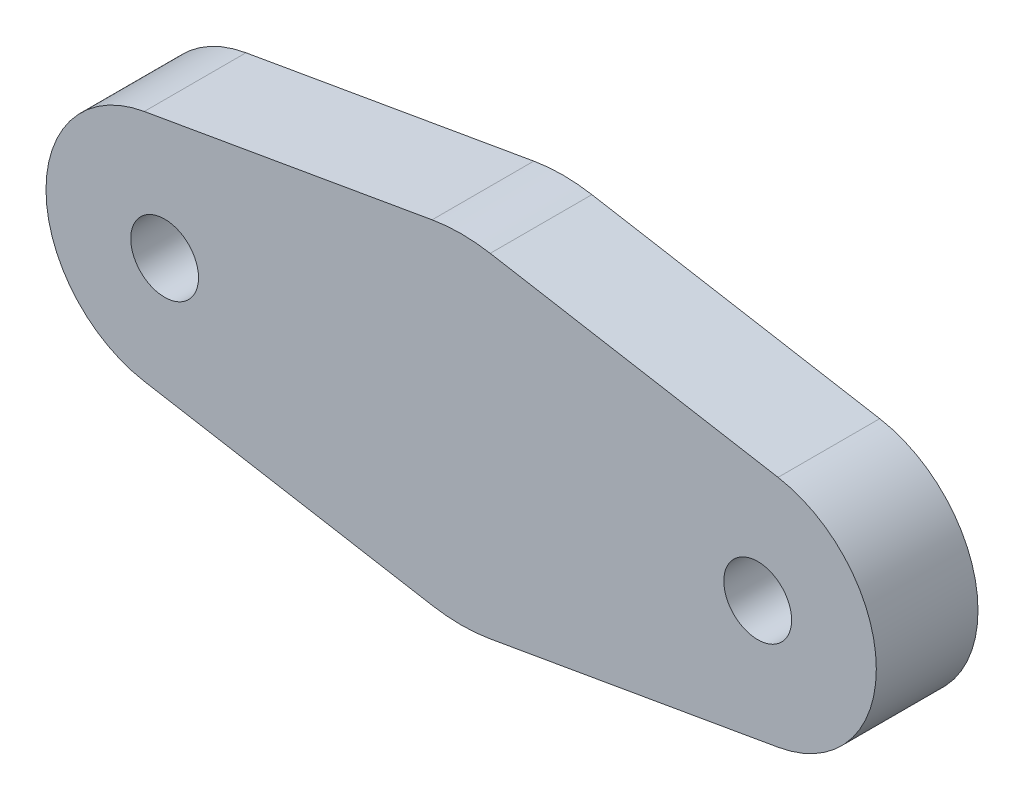
SolidWorks part; units mm, degrees
material "Birch plywood FK"
ref_plane "Спереди" through (0, 0, 0) normal (0, 0, 1) x (1, 0, 0)
ref_plane "Сверху" through (0, 0, 0) normal (0, 1, 0) x (1, 0, 0)
ref_plane "Справа" through (0, 0, 0) normal (1, 0, 0) x (0, 0, -1)
sketch "Эскиз1" plane through (0, 0, 0) normal (0, 0, 1) x (1, 0, 0)
  line L0 (-1.7143, 9.852) -> (-18.7, 6.8964)
  line L1 (-17.5, 0) -> (17.5, 0) construction
  line L2 (18.7, 6.8964) -> (1.7143, 9.852)
  line L3 (18.7, -6.8964) -> (1.7143, -9.852)
  line L6 (-1.7143, -9.852) -> (-18.7, -6.8964)
  arc A0 (-1.7143, -9.852) -> (1.7143, -9.852) centre (0, 0) ccw
  arc A1 (-18.7, 6.8964) -> (-18.7, -6.8964) centre (-17.5, 0) ccw
  arc A2 (18.7, -6.8964) -> (18.7, 6.8964) centre (17.5, 0) ccw
  arc A3 (1.7143, 9.852) -> (-1.7143, 9.852) centre (0, 0) ccw
  circle A4 centre (-17.5, 0) radius 2
  circle A5 centre (17.5, 0) radius 2
  dimension "D1" = 20
  dimension "D3" = 14
  dimension "D4" = 4
  dimension "D2" = 35
extrude "Бобышка-Вытянуть1" add sketch "Эскиз1" along normal blind 6
